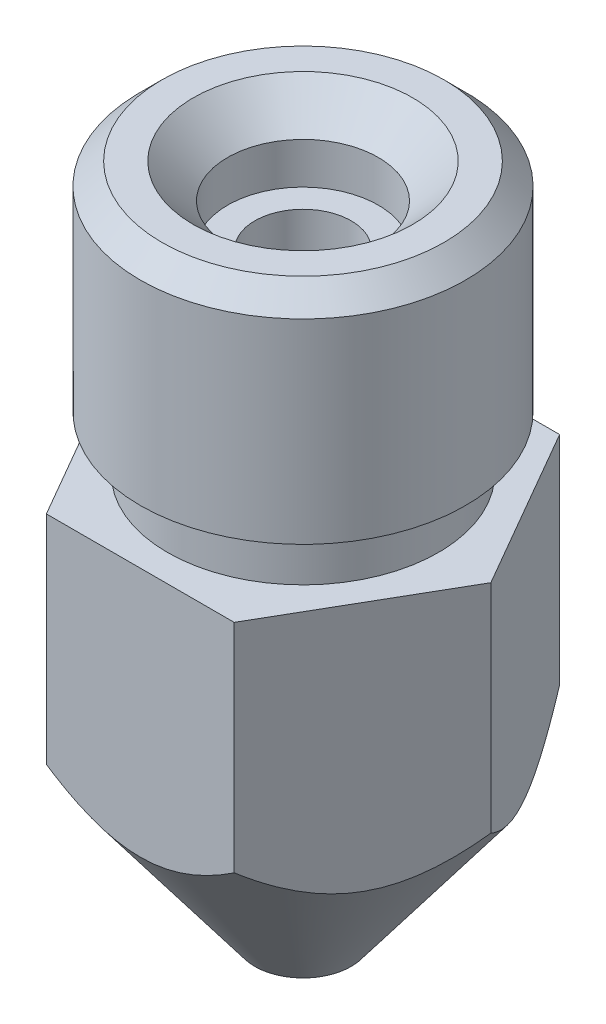
SolidWorks part; units mm, degrees
material "Brass"
ref_plane "Front Plane" through (0, 0, 0) normal (0, 0, 1) x (1, 0, 0)
ref_plane "Top Plane" through (0, 0, 0) normal (0, 1, 0) x (1, 0, 0)
ref_plane "Right Plane" through (0, 0, 0) normal (1, 0, 0) x (0, 0, -1)
sketch "Sketch2" plane through (0, 0, 0) normal (0, 1, 0) x (1, 0, 0)
  circle A0 centre (0, 0) radius 3
  dimension "D1" = 6
extrude "Boss-Extrude1" add sketch "Sketch2" along normal blind 13
sketch "Sketch3" plane through (0, 0, 0) normal (0, -1, 0) x (1, 0, 0)
  line L1 (1.7321, -3) -> (3.4641, 0)
  line L2 (3.4641, 0) -> (1.7321, 3)
  line L3 (1.7321, 3) -> (-1.7321, 3)
  line L4 (-1.7321, 3) -> (-3.4641, 0)
  line L5 (-3.4641, 0) -> (-1.7321, -3)
  line L6 (-1.7321, -3) -> (1.7321, -3)
  circle A0 centre (0, 0) radius 3 construction
  circle A1 centre (0, 0) radius 3 construction
extrude "Boss-Extrude2" add sketch "Sketch3" against normal blind 8
sketch "Sketch4" plane through (0, 0, 0) normal (0, 0, 1) x (1, 0, 0)
  line L0 (-0.45, 0) -> (-3.4641, 4)
  line L1 (-3.4641, 8) -> (-3.4641, 0) construction
  line L2 (-3.4641, 4) -> (-3.4641, 0)
  line L3 (-3.4641, 0) -> (-0.45, 0)
  line L4 (1.7321, 0) -> (-1.7321, 0) construction
  point P5 (0, 0)
  point P8 (0, 0)
  point P9 (-0.2135, 0)
  point P12 (0, 0)
  dimension "D1" = 4
  dimension "D2" = 0.45
sketch "Sketch5" plane through (0, 0, 0) normal (0, 0, 1) x (1, 0, 0)
  line L0 (0, 0) -> (0, 13) construction
revolve "Cut-Revolve3" cut sketch "Sketch4" angle 360 about L0
sketch "Sketch6" plane through (0, 8, 0) normal (0, 1, 0) x (1, 0, 0)
  circle A0 centre (0, 0) radius 2.5
  circle A1 centre (0, 0) radius 3
  dimension "D1" = 5
extrude "Cut-Extrude1" cut sketch "Sketch6" along normal blind 1
chamfer "Chamfer1" distance 0.4 angle 45 1 edges at (0, 13, 3)
sketch "Sketch7" plane through (0, 0, 0) normal (0, -1, 0) x (1, 0, 0)
  circle A0 centre (0, 0) radius 0.2
  dimension "D1" = 0.4
extrude "Cut-Extrude2" cut sketch "Sketch7" against normal through all
hole_wizard "CBORE for #0 Fillister Head Machine Screw1" positions "Sketch8" profile "Sketch9" counterbore size "#0" standard "ANSI Inch" end condition through all
sketch "Sketch8" plane through (0, 13, 0) normal (0, 1, 0) x (-1, 0, 0)
  point P0 (0, 0)
sketch "Sketch9" plane through (0, 13, 0) normal (1, 0, 0) x (0, 0, 1)
  line L0 (0, 0) -> (0, 13)
  line L1 (0, 13) -> (0.889, 13)
  line L3 (0.889, 13) -> (0.889, 1.397)
  line L4 (1.3894, 1.397) -> (0.889, 1.397)
  line L5 (1.3894, 1.397) -> (1.3894, 0.635)
  line L6 (1.3894, 0.635) -> (2.0244, 0)
  line L7 (2.0244, 0) -> (0, 0)
  line L8 (-1.3894, 0.635) -> (-2.0244, 0) construction
  line L11 (0, -6.35) -> (0, 107.95) construction
  dimension "Thru Hole Dia." = 1.778
  dimension "Thru Hole Depth" = 13
  dimension "C'Bore Dia." = 2.7788
  dimension "C'Bore Depth" = 1.397
  dimension "Near C'Sink Dia." = 4.0488
  dimension "Near C'Sink Angle" = 90
